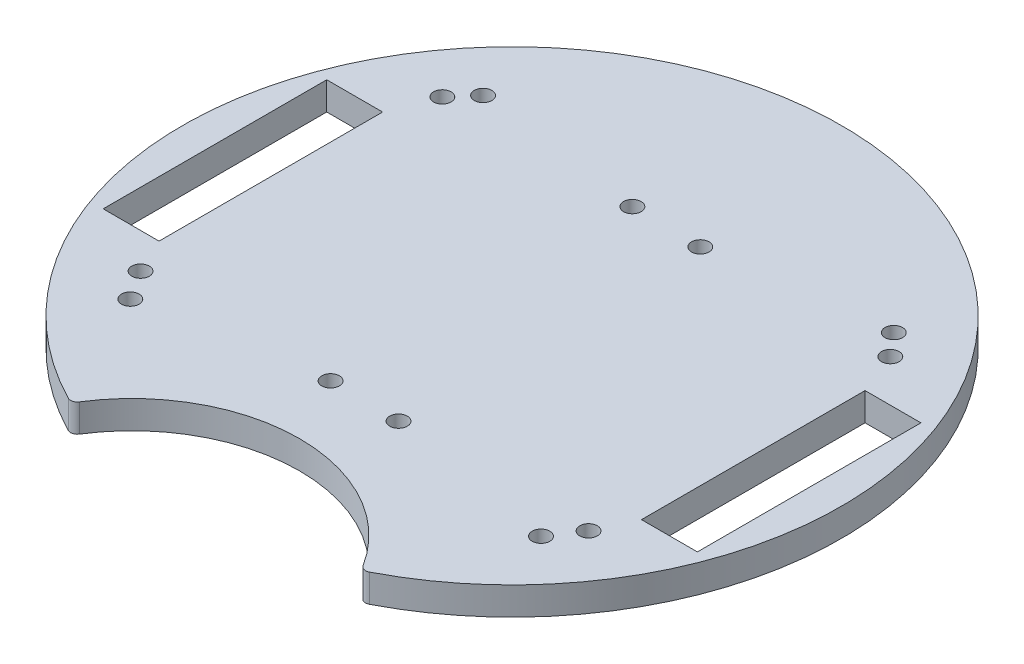
SolidWorks part; units mm, degrees
ref_plane "Front Plane" through (0, 0, 0) normal (0, 0, 1) x (1, 0, 0)
ref_plane "Top Plane" through (0, 0, 0) normal (0, 1, 0) x (1, 0, 0)
ref_plane "Right Plane" through (0, 0, 0) normal (1, 0, 0) x (0, 0, -1)
sketch "Sketch1" plane through (0, 0, 0) normal (0, 1, 0) x (1, 0, 0)
  line L0 (4.0141, -37.434) -> (54.8141, -37.434) construction
  line L1 (-54.8141, -37.2245) -> (-4.0141, -37.2245) construction
  line L2 (-54.8141, -37.2245) -> (-54.8141, 38.9755) construction
  line L3 (-32.9956, -67.352) -> (0, -86.402) construction
  line L4 (32.9956, -67.352) -> (0, -86.402) construction
  line L5 (-54.8141, 38.9755) -> (-4.0141, 38.9755) construction
  line L6 (-4.0141, -37.2245) -> (-4.0141, 38.9755) construction
  line L7 (4.0141, -37.434) -> (4.0141, 38.766) construction
  line L8 (4.0141, 38.766) -> (54.8141, 38.766) construction
  line L9 (54.8141, -25.4) -> (54.8141, 25.4)
  line L10 (-67.5141, -25.4) -> (-54.8141, -25.4)
  line L11 (-67.5141, -25.4) -> (-67.5141, 25.4)
  line L12 (-67.5141, 25.4) -> (-54.8141, 25.4)
  line L13 (-54.8141, 25.4) -> (-54.8141, -25.4)
  line L14 (67.5141, 25.4) -> (54.8141, 25.4)
  line L15 (67.5141, -25.4) -> (67.5141, 25.4)
  line L16 (67.5141, -25.4) -> (54.8141, -25.4)
  line L17 (54.8141, -37.434) -> (54.8141, 38.766) construction
  circle A0 centre (-51.0041, -33.4145) radius 2
  arc A1 (32.2407, -66.1006) -> (-32.2407, -66.1006) centre (0, -86.402) ccw
  arc A2 (34.1948, -66.6358) -> (-34.1948, -66.6358) centre (0, 0) ccw
  circle A3 centre (7.8241, -33.624) radius 2
  circle A4 centre (51.0041, -33.624) radius 2
  circle A5 centre (51.0041, 34.956) radius 2
  circle A6 centre (-7.8241, 35.1655) radius 2
  circle A7 centre (-7.8241, -33.4145) radius 2
  circle A25 centre (-51.0041, 35.1655) radius 2
  circle A38 centre (-46.6637, -40.0812) radius 2
  circle A39 centre (46.6637, -40.0812) radius 2
  circle A40 centre (46.6637, 40.0812) radius 2
  circle A41 centre (-46.6637, 40.0812) radius 2
  arc A42 (-34.1948, -66.6358) -> (-32.2407, -66.1006) centre (-33.51, -65.3013) ccw
  arc A43 (34.1948, -66.6358) -> (32.2407, -66.1006) centre (33.51, -65.3013) cw
  circle A47 centre (7.8241, 34.956) radius 2
  dimension "D3" = 120
  dimension "D2" = 76.2
  dimension "D10" = 0
  dimension "D11" = 3.81
  dimension "D15" = 3.81
  dimension "D17" = 3.81
  dimension "D18" = 3.81
  dimension "D12" = 4
  dimension "D6" = 50.8
  dimension "D4" = 50.8
  dimension "D5" = 12.7
  dimension "D7" = 76.2
  dimension "D8" = 50.8
  dimension "D9" = 0
  dimension "D13" = 3.81
  dimension "D14" = 3.81
  dimension "D16" = 3.81
  dimension "D19" = 3.81
  dimension "D20" = 3.81
  dimension "D21" = 3.81
  dimension "D22" = 3.81
  dimension "D23" = 3.81
  dimension "D24" = 3.81
  dimension "D25" = 3.81
  dimension "D26" = 3.81
  dimension "D27" = 3.81
extrude "Boss-Extrude3" add sketch "Sketch1" along normal blind 6.35
